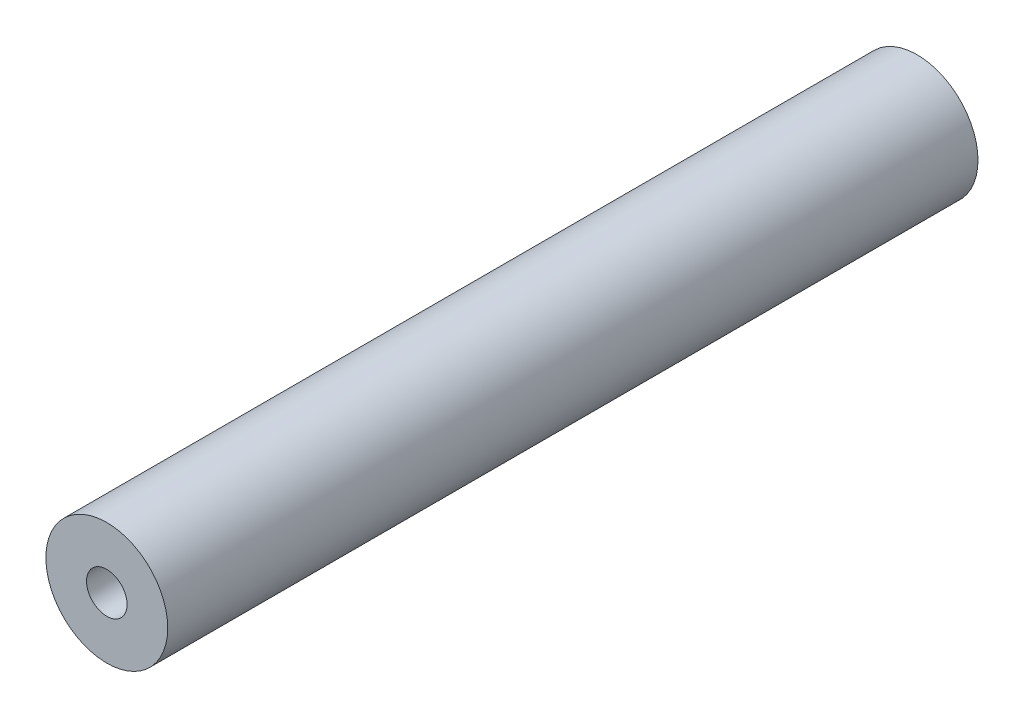
SolidWorks part; units mm, degrees
ref_plane "Front Plane" through (0, 0, 0) normal (0, 0, 1) x (1, 0, 0)
ref_plane "Top Plane" through (0, 0, 0) normal (0, 1, 0) x (1, 0, 0)
ref_plane "Right Plane" through (0, 0, 0) normal (1, 0, 0) x (0, 0, -1)
sketch "Sketch1" plane through (0, 0, 0) normal (0, 0, 1) x (1, 0, 0)
  circle A0 centre (0, 0) radius 3.81
  circle A1 centre (0, 0) radius 1.27
  dimension "D1" = 7.62
  dimension "D2" = 2.54
extrude "Boss-Extrude1" add sketch "Sketch1" against normal blind 50.673
